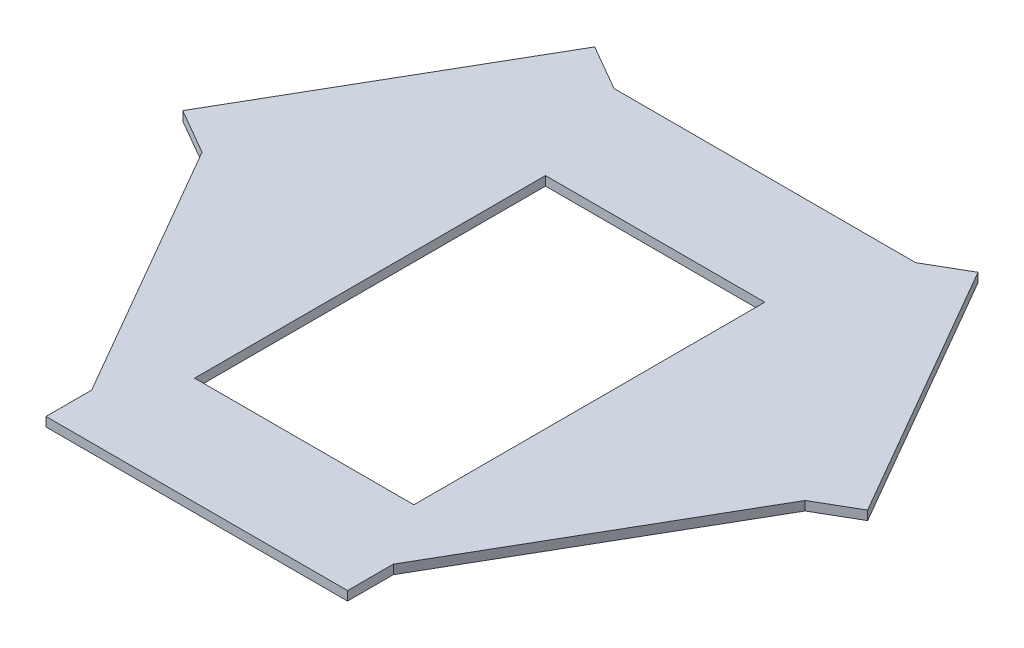
SolidWorks part; units mm, degrees
ref_plane "Front Plane" through (0, 0, 0) normal (0, 0, 1) x (1, 0, 0)
ref_plane "Top Plane" through (0, 0, 0) normal (0, 1, 0) x (1, 0, 0)
ref_plane "Right Plane" through (0, 0, 0) normal (1, 0, 0) x (0, 0, -1)
sketch "Sketch1" plane through (0, 0, 0) normal (0, 1, 0) x (1, 0, 0)
  line L0 (-82.5, 142.8942) -> (-165, 0)
  line L1 (82.5, -142.8942) -> (165, 0)
  line L2 (165, 0) -> (82.5, 142.8942)
  line L3 (82.5, 142.8942) -> (-82.5, 142.8942)
  line L4 (-82.5, 142.8942) -> (-165, 0)
  line L5 (-165, 0) -> (-82.5, -142.8942)
  line L6 (-82.5, -142.8942) -> (82.5, -142.8942)
  line L7 (-82.5, 142.8942) -> (-107.5, 157.3279)
  line L8 (-165, 0) -> (-190, 14.4338)
  line L9 (-107.5, 157.3279) -> (-190, 14.4338)
  line L10 (82.5, 142.8942) -> (165, 0)
  line L11 (82.5, 142.8942) -> (104.1506, 155.3942)
  line L12 (165, 0) -> (186.6506, 12.5)
  line L13 (104.1506, 155.3942) -> (186.6506, 12.5)
  line L14 (-82.5, -142.8942) -> (82.5, -142.8942)
  line L15 (-82.5, -142.8942) -> (-82.5, -167.8942)
  line L16 (82.5, -142.8942) -> (82.5, -167.8942)
  line L17 (-82.5, -167.8942) -> (82.5, -167.8942)
  line L18 (-60, 82.8942) -> (60, 82.8942)
  line L19 (-60, 82.8942) -> (-60, -109.1058)
  line L20 (60, 82.8942) -> (60, -109.1058)
  line L21 (-60, -109.1058) -> (60, -109.1058)
  circle A0 centre (0, 0) radius 142.8942 construction
  dimension "D1" = 165
  dimension "D2" = 25
  dimension "D3" = 25
  dimension "D4" = 25
  dimension "D5" = 120
  dimension "D6" = 192
  dimension "D7" = 60
  dimension "D8" = 33.7884
  dimension "D9" = 105
extrude "Boss-Extrude2" add sketch "Sketch1" along normal blind 5 contours L5 L6 L1 L2 L3 L0 L21 L19 L18 L20 | L7 L9 L8 L0 | L13 L11 L2 L12 | L15 L17 L16 L6
